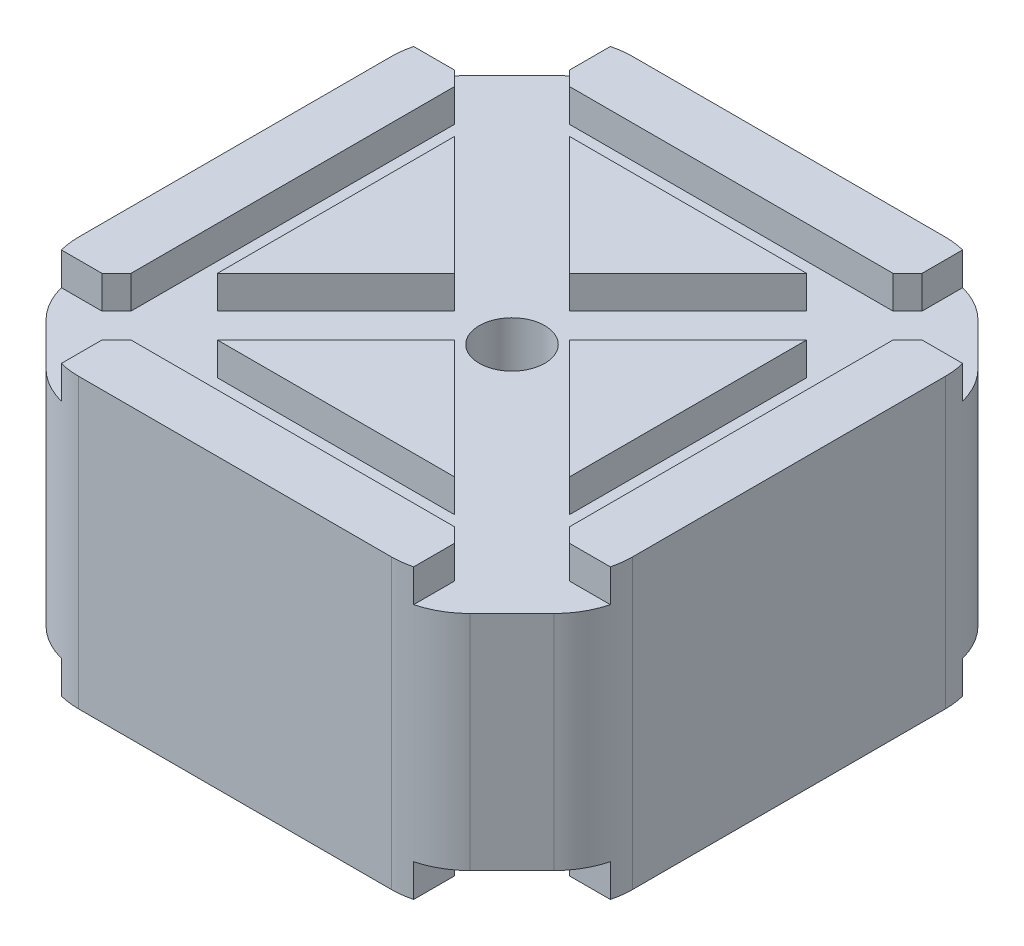
SolidWorks part; units mm, degrees
material "Alumina"
ref_plane "Front Plane" through (0, 0, 0) normal (0, 0, 1) x (1, 0, 0)
ref_plane "Top Plane" through (0, 0, 0) normal (0, 1, 0) x (1, 0, 0)
ref_plane "Right Plane" through (0, 0, 0) normal (1, 0, 0) x (0, 0, -1)
sketch "Sketch1" plane through (0, 0, 0) normal (0, 1, 0) x (1, 0, 0)
  line L0 (-21.15, 16.7509) -> (-16.7509, 21.15)
  line L1 (-16.7509, -21.15) -> (16.7509, -21.15)
  line L2 (-21.15, -16.7509) -> (-21.15, 16.7509)
  line L3 (-16.7509, 21.15) -> (16.7509, 21.15)
  line L4 (21.15, -16.7509) -> (21.15, 16.7509)
  line L7 (16.7509, 21.15) -> (21.15, 16.7509)
  line L8 (16.7509, -21.15) -> (21.15, -16.7509)
  line L9 (-21.15, -16.7509) -> (-16.7509, -21.15)
  point P0 (0, 0)
  dimension "D1" = 42.3
  dimension "D2" = 42.3
  dimension "D3" = 53.6
  dimension "D4" = 45
  dimension "D5" = 45
  dimension "D7" = 53.6
extrude "Boss-Extrude1" add sketch "Sketch1" along normal blind 11
sketch "Sketch18" plane through (0, 0, 21.15) normal (0, 0, 1) x (1, 0, 0)
  line L0 (13.4509, 11) -> (13.4509, 8.5)
  line L1 (-16.7509, 11) -> (16.7509, 11) construction
  line L2 (13.4509, 8.5) -> (16.7509, 8.5)
  line L3 (16.7509, 11) -> (16.7509, 0) construction
  line L4 (16.7509, 8.5) -> (16.7509, 11)
  line L5 (16.7509, 11) -> (13.4509, 11)
  line L6 (-13.4509, 11) -> (-13.4509, 8.5)
  line L7 (-13.4509, 8.5) -> (-16.7509, 8.5)
  line L8 (-16.7509, 11) -> (-16.7509, 0) construction
  line L9 (-16.7509, 8.5) -> (-16.7509, 11)
  line L10 (-16.7509, 11) -> (-13.4509, 11)
  dimension "D1" = 2.5
  dimension "D2" = 2.5
  dimension "D3" = 3.3
  dimension "D4" = 3.3
extrude "Cut-Extrude10" cut sketch "Sketch18" against normal through all
sketch "Sketch19" plane through (21.15, 0, 0) normal (1, 0, 0) x (0, 0, -1)
  line L0 (-13.4509, 11) -> (-13.4509, 8.5)
  line L1 (-16.7509, 11) -> (16.7509, 11) construction
  line L2 (-13.4509, 8.5) -> (-16.7509, 8.5)
  line L3 (-16.7509, 11) -> (-16.7509, 0) construction
  line L4 (-16.7509, 8.5) -> (-16.7509, 11)
  line L5 (-16.7509, 11) -> (-13.4509, 11)
  line L6 (13.4509, 11) -> (13.4509, 8.5)
  line L7 (13.4509, 8.5) -> (16.7509, 8.5)
  line L8 (16.7509, 11) -> (16.7509, 0) construction
  line L9 (16.7509, 8.5) -> (16.7509, 11)
  line L10 (16.7509, 11) -> (13.4509, 11)
  dimension "D1" = 3.3
  dimension "D2" = 3.3
  dimension "D3" = 2.5
  dimension "D4" = 2.5
extrude "Cut-Extrude11" cut sketch "Sketch19" against normal through all
sketch "Sketch20" plane through (18.9505, 0, 18.9505) normal (0.7071, 0, 0.7071) x (0.7071, 0, -0.7071)
  line L0 (-3.1106, 8.5) -> (3.1106, 8.5)
  line L1 (3.1106, 8.5) -> (3.1106, 11)
  line L2 (3.1106, 11) -> (-3.1106, 11)
  line L3 (-3.1106, 11) -> (-3.1106, 8.5)
extrude "Cut-Extrude12" cut sketch "Sketch20" against normal through all
sketch "Sketch21" plane through (-18.9505, 0, 18.9505) normal (-0.7071, 0, 0.7071) x (0.7071, 0, 0.7071)
  line L0 (-3.1106, 8.5) -> (3.1106, 8.5)
  line L1 (3.1106, 8.5) -> (3.1106, 11)
  line L2 (3.1106, 11) -> (-3.1106, 11)
  line L3 (-3.1106, 11) -> (-3.1106, 8.5)
extrude "Cut-Extrude13" cut sketch "Sketch21" against normal through all
sketch "Sketch22" plane through (0, 8.5, 0) normal (0, 1, 0) x (1, 0, 0)
  circle A0 centre (0, 0) radius 2.5
  dimension "D1" = 5
extrude "Cut-Extrude14" cut sketch "Sketch22" against normal through all
mirror "Mirror1" about plane through (0, 0, 0) normal (0, -1, 0) of "Boss-Extrude1", "Cut-Extrude14", "Cut-Extrude13", "Cut-Extrude12", "Cut-Extrude11", "Cut-Extrude10"
sketch "Sketch23" plane through (0, 8.5, 0) normal (0, 1, 0) x (1, 0, 0)
  line L0 (-21.15, -14.4325) -> (-14.4325, -21.15)
  line L1 (-14.4325, -21.15) -> (-16.7509, -21.15)
  line L2 (-16.7509, -21.15) -> (-21.15, -16.7509)
  line L3 (-21.15, -16.7509) -> (-21.15, -14.4325)
  line L4 (-21.15, 14.4325) -> (-14.4325, 21.15)
  line L5 (-14.4325, 21.15) -> (-16.7509, 21.15)
  line L6 (-16.7509, 21.15) -> (-21.15, 16.7509)
  line L7 (-21.15, 16.7509) -> (-21.15, 14.4325)
  line L8 (14.4325, 21.15) -> (21.15, 14.4325)
  line L9 (21.15, 14.4325) -> (21.15, 16.7509)
  line L10 (21.15, 16.7509) -> (16.7509, 21.15)
  line L11 (16.7509, 21.15) -> (14.4325, 21.15)
  line L12 (14.4325, -21.15) -> (21.15, -14.4325)
  line L13 (21.15, -14.4325) -> (21.15, -16.7509)
  line L14 (21.15, -16.7509) -> (16.7509, -21.15)
  line L15 (16.7509, -21.15) -> (14.4325, -21.15)
  dimension "D1" = 9.5
  dimension "D2" = 9.5
  dimension "D3" = 9.5
  dimension "D4" = 9.5
extrude "Cut-Extrude15" cut sketch "Sketch23" against normal through all
fillet "Fillet8" radius 6 8 edges at (14.4325, 0, -21.15) (21.15, 0, -14.4325) (-21.15, 0, -14.4325) (-14.4325, 0, -21.15) (-14.4325, 0, 21.15) (-21.15, 0, 14.4325) (21.15, 0, 14.4325) (14.4325, 0, 21.15)
